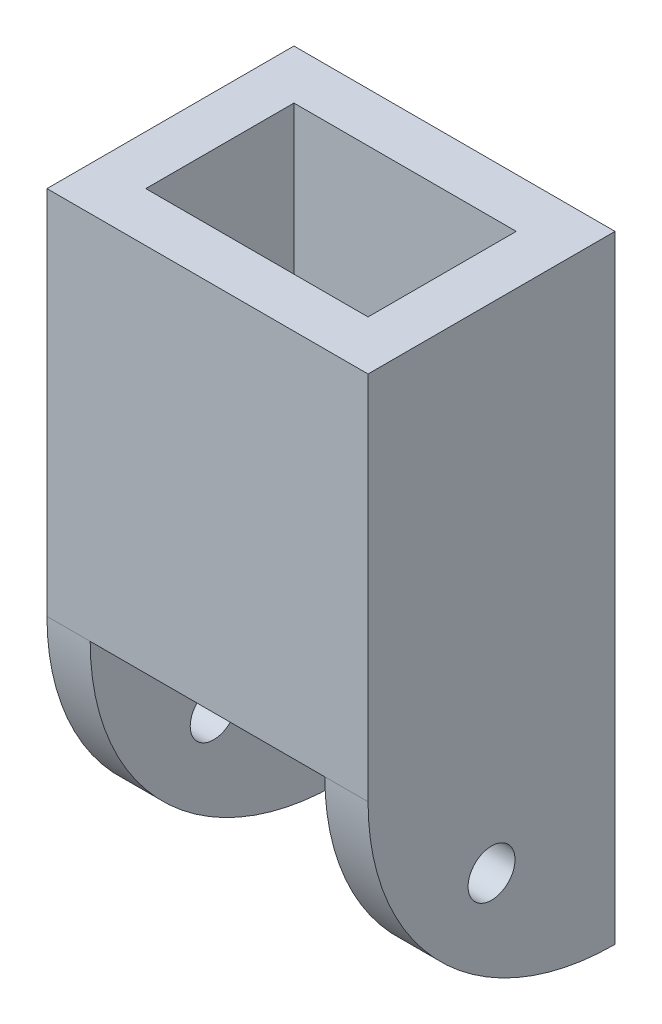
SolidWorks part; units mm, degrees
ref_plane "Front Plane" through (0, 0, 0) normal (0, 0, 1) x (1, 0, 0)
ref_plane "Top Plane" through (0, 0, 0) normal (0, 1, 0) x (1, 0, 0)
ref_plane "Right Plane" through (0, 0, 0) normal (1, 0, 0) x (0, 0, -1)
sketch "Sketch1" plane through (0, 0, 0) normal (0, 1, 0) x (1, 0, 0)
  line L1 (-6.5, -5) -> (6.5, -5)
  line L2 (-6.5, -5) -> (-6.5, 5)
  line L3 (-6.5, 5) -> (6.5, 5)
  line L4 (6.5, -5) -> (6.5, 5)
  line L5 (-6.5, -5) -> (6.5, 5) construction
  line L6 (-6.5, 5) -> (6.5, -5) construction
  line L7 (-4.5, -3) -> (4.5, -3)
  line L8 (-4.5, -3) -> (-4.5, 3)
  line L9 (-4.5, 3) -> (4.5, 3)
  line L10 (4.5, -3) -> (4.5, 3)
  line L11 (-4.5, -3) -> (4.5, 3) construction
  line L12 (-4.5, 3) -> (4.5, -3) construction
  point P0 (0, 0)
  point P6 (0, 0)
  dimension "D1" = 10
  dimension "D2" = 13
  dimension "D3" = 2
  dimension "D4" = 2
extrude "Boss-Extrude1" add sketch "Sketch1" along normal blind 15
sketch "Sketch2" plane through (6.5, 0, 0) normal (1, 0, 0) x (0, 0, -1)
  line L0 (5, 0) -> (5, -10)
  line L2 (-5, 0) -> (5, 0)
  arc A0 (-5, 0) -> (5, -10) centre (5, 0) ccw
  line M2 (-5, 0) -> (5, 0)
  dimension "D1" = 10
extrude "Boss-Extrude2" add sketch "Sketch2" against normal blind 2 contours A0 L0 M2
mirror "Mirror1" about plane through (0, 0, 0) normal (1, 0, 0) of "Boss-Extrude2"
sketch "Sketch3" plane through (6.5, 0, 0) normal (1, 0, 0) x (0, 0, -1)
  line L0 (5.5, 0) -> (-5.5, 0) construction
  line L1 (5, 15) -> (5, -10) construction
  circle A0 centre (0, -5) radius 0.95
  dimension "D1" = 1.9
  dimension "D2" = 5
  dimension "D3" = 5
extrude "Cut-Extrude1" cut sketch "Sketch3" against normal through all
sketch "Sketch5" plane through (0, 0, 0) normal (0, 0, 1) x (1, 0, 0)
  line L0 (5.5, 0) -> (-5.5, 0) construction
  line L1 (-4.5, -10) -> (-4.75, -10)
  line L2 (-4.5, -10) -> (-4.5, 0)
  line L3 (-4.5, 0) -> (-4.75, 0)
  line L4 (-4.75, -10) -> (-4.75, 0)
  line L6 (4.5, -10) -> (4.75, -10)
  line L7 (4.5, -10) -> (4.5, 0)
  line L8 (4.5, 0) -> (4.75, 0)
  line L9 (4.75, -10) -> (4.75, 0)
  dimension "D1" = 0.25
  dimension "D2" = 0.25
extrude "Cut-Extrude3" cut sketch "Sketch5" against normal through all both and the other way through all
sketch "Sketch6" plane through (0, 0, 0) normal (0, -1, 0) x (1, 0, 0)
  line L0 (0, -5.5) -> (0, 5.5) construction
  line L1 (-4, 3.6) -> (4, 3.6)
  line L2 (-4, 3.6) -> (-4, 4.4)
  line L3 (-4, 4.4) -> (4, 4.4)
  line L4 (4, 3.6) -> (4, 4.4)
  line L5 (-4, 3.6) -> (4, 4.4) construction
  line L6 (-4, 4.4) -> (4, 3.6) construction
  line L7 (-4.75, 5) -> (4.75, 5) construction
  point P0 (0, 4)
  dimension "D1" = 1
  dimension "D2" = 0.8
  dimension "D3" = 8
extrude "Cut-Extrude4" cut sketch "Sketch6" against normal blind 10
mirror "Mirror2" about plane through (0, 0, 0) normal (0, 0, 1) of "Cut-Extrude4"
